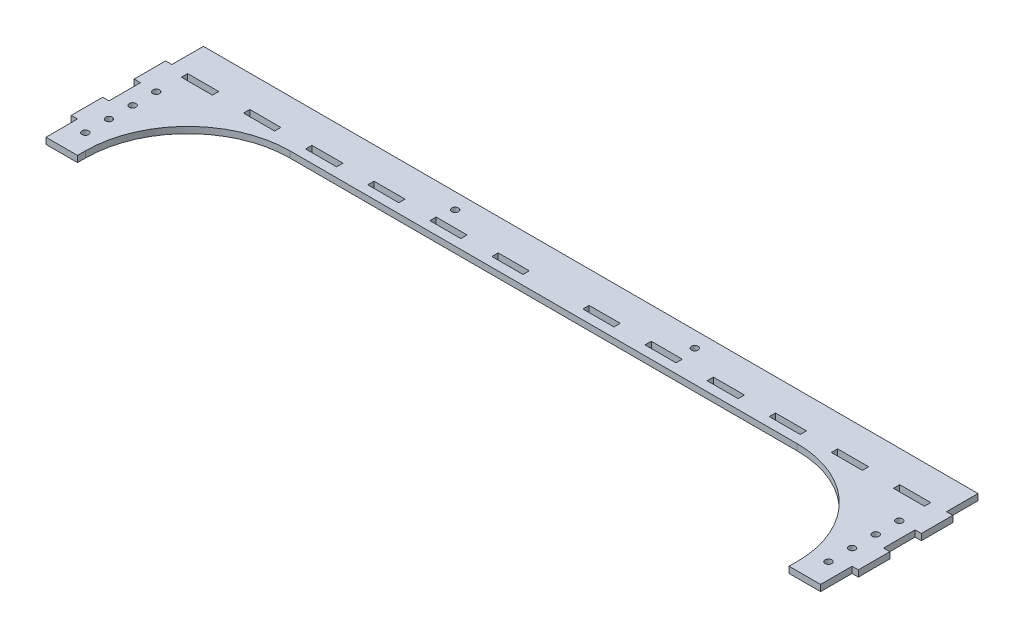
SolidWorks part; units mm, degrees
ref_plane "Front Plane" through (0, 0, 0) normal (0, 0, 1) x (1, 0, 0)
ref_plane "Top Plane" through (0, 0, 0) normal (0, 1, 0) x (1, 0, 0)
ref_plane "Right Plane" through (0, 0, 0) normal (1, 0, 0) x (0, 0, -1)
sketch "Sketch1" plane through (0, 0, 0) normal (0, 1, 0) x (1, 0, 0)
  line L0 (0, -24.6267) -> (0, 100.5806) construction
  line L1 (4, 0) -> (4, 20)
  line L2 (4, 20) -> (0, 20)
  line L3 (0, 20) -> (0, 40)
  line L4 (0, 40) -> (4, 40)
  line L5 (4, 40) -> (4, 60)
  line L6 (4, 60) -> (0, 60)
  line L7 (0, 60) -> (0, 80)
  line L8 (0, 80) -> (4, 80)
  line L9 (4, 80) -> (4, 100)
  line L10 (0, 0) -> (4, 0) construction
  line L11 (4, 0) -> (24, 0)
  line L12 (24, 0) -> (24, 5)
  line L13 (89, 70) -> (411, 70)
  line L16 (251.0496, 76) -> (-35.0505, 76) construction
  line L17 (14, 0) -> (14, 49.3314) construction
  line L18 (53.45, 76) -> (53.45, 80)
  line L19 (14, 76) -> (33.725, 76)
  line L20 (14, 76) -> (14, 80)
  line L21 (14, 80) -> (33.725, 80)
  line L22 (33.725, 76) -> (33.725, 80)
  line L23 (53.45, 76) -> (73.175, 76)
  line L24 (73.175, 76) -> (73.175, 80)
  line L25 (53.45, 80) -> (73.175, 80)
  line L26 (92.9, 76) -> (92.9, 80)
  line L27 (92.9, 76) -> (112.625, 76)
  line L28 (112.625, 76) -> (112.625, 80)
  line L29 (92.9, 80) -> (112.625, 80)
  line L30 (132.35, 76) -> (132.35, 80)
  line L31 (132.35, 76) -> (152.075, 76)
  line L32 (152.075, 76) -> (152.075, 80)
  line L33 (132.35, 80) -> (152.075, 80)
  line L34 (171.8, 76) -> (171.8, 80)
  line L35 (171.8, 76) -> (191.525, 76)
  line L36 (191.525, 76) -> (191.525, 80)
  line L37 (171.8, 80) -> (191.525, 80)
  line L38 (211.25, 76) -> (211.25, 80)
  line L39 (211.25, 76) -> (230.975, 76)
  line L40 (230.975, 76) -> (230.975, 80)
  line L41 (211.25, 80) -> (230.975, 80)
  line L42 (228.5555, 90) -> (146.8646, 90) construction
  line L43 (250, 70) -> (250, 140.3677) construction
  line L53 (4, 100) -> (250, 100)
  line L54 (271.4445, 90) -> (353.1354, 90) construction
  line L55 (486, 0) -> (486, 49.3314) construction
  line L56 (248.9504, 76) -> (535.0505, 76) construction
  line L57 (500, 0) -> (496, 0) construction
  line L58 (500, -24.6267) -> (500, 100.5806) construction
  line L59 (250, 100) -> (496, 100)
  line L60 (288.75, 80) -> (269.025, 80)
  line L61 (269.025, 76) -> (269.025, 80)
  line L62 (288.75, 76) -> (269.025, 76)
  line L63 (288.75, 76) -> (288.75, 80)
  line L64 (328.2, 80) -> (308.475, 80)
  line L65 (308.475, 76) -> (308.475, 80)
  line L66 (328.2, 76) -> (308.475, 76)
  line L67 (328.2, 76) -> (328.2, 80)
  line L68 (367.65, 80) -> (347.925, 80)
  line L69 (347.925, 76) -> (347.925, 80)
  line L70 (367.65, 76) -> (347.925, 76)
  line L71 (367.65, 76) -> (367.65, 80)
  line L72 (407.1, 80) -> (387.375, 80)
  line L73 (387.375, 76) -> (387.375, 80)
  line L74 (407.1, 76) -> (387.375, 76)
  line L75 (407.1, 76) -> (407.1, 80)
  line L76 (446.55, 80) -> (426.825, 80)
  line L77 (426.825, 76) -> (426.825, 80)
  line L78 (446.55, 76) -> (426.825, 76)
  line L79 (466.275, 76) -> (466.275, 80)
  line L80 (486, 80) -> (466.275, 80)
  line L81 (486, 76) -> (486, 80)
  line L82 (486, 76) -> (466.275, 76)
  line L83 (446.55, 76) -> (446.55, 80)
  line L84 (476, 0) -> (476, 5)
  line L85 (496, 0) -> (476, 0)
  line L86 (496, 80) -> (496, 100)
  line L87 (500, 80) -> (496, 80)
  line L88 (500, 60) -> (500, 80)
  line L89 (496, 60) -> (500, 60)
  line L90 (496, 40) -> (496, 60)
  line L91 (500, 40) -> (496, 40)
  line L92 (500, 20) -> (500, 40)
  line L93 (496, 20) -> (500, 20)
  line L94 (496, 0) -> (496, 20)
  line L95 (-5.4693, 37.5) -> (40.2804, 37.5) construction
  circle A0 centre (14, 15) radius 2.125
  circle A1 centre (14, 30) radius 2.125
  circle A10 centre (173.885, 90) radius 2.125
  circle A11 centre (326.115, 90) radius 2.125
  circle A12 centre (486, 30) radius 2.125
  circle A13 centre (486, 15) radius 2.125
  arc A14 (476, 5) -> (411, 70) centre (411, 5) ccw
  arc A15 (24, 5) -> (89, 70) centre (89, 5) cw
  circle A16 centre (14, 60) radius 2.125
  circle A17 centre (14, 45) radius 2.125
  circle A18 centre (486, 45) radius 2.125
  circle A19 centre (486, 60) radius 2.125
  point P61 (250, 100)
  point P62 (476, 70)
  point P112 (24, 70)
  dimension "D8" = 4.25
  dimension "D14" = 4.25
  dimension "D15" = 65
  dimension "D1" = 20
  dimension "D2" = 30
  dimension "D3" = 4
  dimension "D4" = 20
  dimension "D5" = 246
  dimension "D6" = 100
  dimension "D7" = 6
  dimension "D9" = 15
  dimension "D10" = 15
  dimension "D11" = 10
  dimension "D12" = 19.725
  dimension "D13" = 4
  dimension "D16" = 7.5
  dimension "D18" = 6
extrude "Boss-Extrude1" add sketch "Sketch1" along normal blind 4
